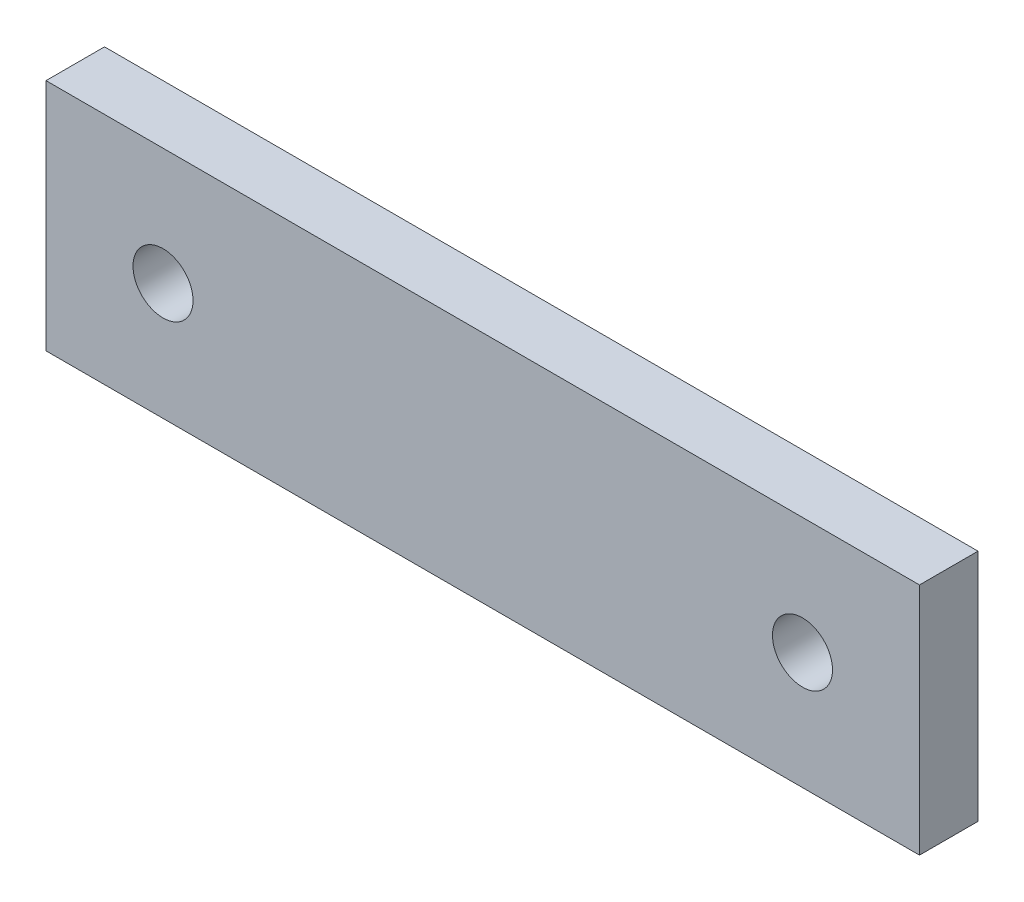
SolidWorks part; units mm, degrees
ref_plane "Front Plane" through (0, 0, 0) normal (0, 0, 1) x (1, 0, 0)
ref_plane "Top Plane" through (0, 0, 0) normal (0, 1, 0) x (1, 0, 0)
ref_plane "Right Plane" through (0, 0, 0) normal (1, 0, 0) x (0, 0, -1)
sketch "Sketch1" plane through (0, 0, 0) normal (0, 0, 1) x (1, 0, 0)
  line L0 (-34.7, 0) -> (34.7, 0) construction
  line L1 (-47.4, -12.7) -> (47.4, -12.7)
  line L2 (-47.4, -12.7) -> (-47.4, 12.7)
  line L3 (-47.4, 12.7) -> (47.4, 12.7)
  line L4 (47.4, -12.7) -> (47.4, 12.7)
  line L5 (-47.4, -12.7) -> (47.4, 12.7) construction
  line L6 (-47.4, 12.7) -> (47.4, -12.7) construction
  circle A0 centre (34.7, 0) radius 3.2576
  circle A1 centre (-34.7, 0) radius 3.2576
  point P0 (0, 0)
  point P9 (0, 0)
  dimension "D1" = 94.8
  dimension "D4" = 6.5151
  dimension "D2" = 12.7
  dimension "D3" = 25.4
extrude "Boss-Extrude1" add sketch "Sketch1" along normal blind 6.35
